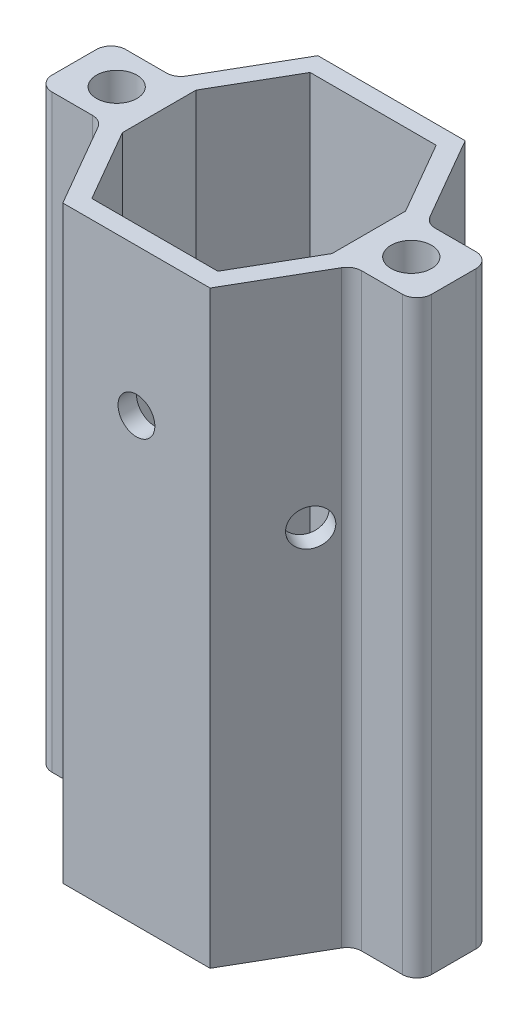
SolidWorks part; units mm, degrees
ref_plane "Front Plane" through (0, 0, 0) normal (0, 0, 1) x (1, 0, 0)
ref_plane "Top Plane" through (0, 0, 0) normal (0, 1, 0) x (1, 0, 0)
ref_plane "Right Plane" through (0, 0, 0) normal (1, 0, 0) x (0, 0, -1)
sketch "Sketch2" plane through (0, 0, 0) normal (0, 1, 0) x (1, 0, 0)
  line L0 (-12.7, 21.997) -> (12.7, 21.997)
  line L17 (12.7, 21.997) -> (25.4, 0)
  line L18 (25.4, 0) -> (12.7, -21.997)
  line L23 (12.7, -21.997) -> (-12.7, -21.997)
  line L24 (-12.7, -21.997) -> (-25.4, 0)
  line L25 (-25.4, 0) -> (-12.7, 21.997)
  line L26 (-10.8669, 18.822) -> (10.8669, 18.822)
  line L27 (10.8669, 18.822) -> (21.7338, 0)
  line L28 (21.7338, 0) -> (10.8669, -18.822)
  line L29 (10.8669, -18.822) -> (-10.8669, -18.822)
  line L30 (-10.8669, -18.822) -> (-21.7338, 0)
  line L31 (-21.7338, 0) -> (-10.8669, 18.822)
  line L32 (-25.4, 0) -> (25.4, 0) construction
  line L34 (-18.0677, -6.35) -> (-32.7323, -6.35)
  line L35 (-18.0677, -6.35) -> (-18.0677, 6.35)
  line L36 (-18.0677, 6.35) -> (-32.7323, 6.35)
  line L37 (-32.7323, -6.35) -> (-32.7323, 6.35)
  line L38 (-18.0677, -6.35) -> (-32.7323, 6.35) construction
  line L39 (-18.0677, 6.35) -> (-32.7323, -6.35) construction
  line L40 (18.0677, -6.35) -> (32.7323, -6.35)
  line L41 (18.0677, -6.35) -> (18.0677, 6.35)
  line L42 (18.0677, 6.35) -> (32.7323, 6.35)
  line L43 (32.7323, -6.35) -> (32.7323, 6.35)
  line L44 (18.0677, -6.35) -> (32.7323, 6.35) construction
  line L45 (18.0677, 6.35) -> (32.7323, -6.35) construction
  circle A0 centre (25.4, 0) radius 3.4925
  circle A1 centre (-25.4, 0) radius 3.4925
  point P0 (0, 0)
  point P3 (0, 21.997)
  point P5 (0, 0)
  point P20 (0, 0)
  point P29 (0, 0)
  dimension "D1" = 25.4
  dimension "D2" = 120
  dimension "D4" = 6.985
  dimension "D3" = 3.175
  dimension "D5" = 50.8
  dimension "D6" = 12.7
extrude "Boss-Extrude1" add sketch "Sketch2" along normal blind 101.6 contours A1 L25 L36 L37 L34 L24 | A0 L18 L40 L43 L42 L17 | L27 L42 L17 L0 L25 L36 L31 L26 | L40 L28 L29 L30 L34 L24 L23 L18 | A1 L24 L34 L30 L31 L36 L25 | L30 L35 L31 | A0 L17 L42 L27 L28 L40 L18 | L41 L28 L27
fillet "Fillet1" radius 2.54 8 edges at (-21.7338, 50.8, -6.35) (-32.7323, 50.8, -6.35) (-32.7323, 50.8, 6.35) (-21.7338, 50.8, 6.35) (21.7338, 50.8, 6.35) (32.7323, 50.8, 6.35) (32.7323, 50.8, -6.35) (21.7338, 50.8, -6.35)
sketch "Sketch9" plane through (0, 0, -21.997) normal (0, 0, 1) x (1, 0, 0)
  line L0 (-6.35, 6.35) -> (-6.35, 24.13) construction
  line L2 (-12.7, 0) -> (-21.0006, 0) construction
  line L4 (0, -24.1967) -> (0, 24.1967) construction
  circle A0 centre (-6.35, 6.35) radius 1
  circle A1 centre (-6.35, 24.13) radius 1
  circle A2 centre (6.35, 6.35) radius 1
  circle A3 centre (6.35, 24.13) radius 1
  circle A4 centre (-6.35, 49.53) radius 1
  circle A5 centre (-6.35, 31.75) radius 1
  circle A6 centre (6.35, 49.53) radius 1
  circle A7 centre (6.35, 31.75) radius 1
  dimension "D1" = 2
  dimension "D2" = 17.78
  dimension "D3" = 6.35
  dimension "D4" = 6.35
  dimension "D5" = 2
extrude "Cut-Extrude7" cut sketch "Sketch9" along normal up to surface (3.175 mm away) up to face at (0, 50.8, -18.822)
sketch "Sketch11" plane through (0, 0, -21.997) normal (0, 0, -1) x (-1, 0, 0)
  line L0 (12.7, 101.6) -> (-12.7, 101.6) construction
  circle A0 centre (0, 76.2) radius 3.175
  point P4 (0, 88.9)
  point P5 (0, 101.6)
  dimension "D2" = 6.35
  dimension "D1" = 25.4
extrude "Cut-Extrude8" cut sketch "Sketch11" against normal through all
sketch "Sketch12" plane through (-19.05, 0, -10.9985) normal (-0.866, 0, -0.5) x (-0.5, 0, 0.866)
  line L0 (3.9012, 101.6) -> (-12.7, 101.6) construction
  line L1 (-12.7, 101.6) -> (-12.7, 0) construction
  circle A0 centre (0, 63.5) radius 3.175
  point P2 (0, 0)
  dimension "D2" = 6.35
  dimension "D1" = 38.1
  dimension "D3" = 12.7
extrude "Cut-Extrude9" cut sketch "Sketch12" against normal through all
sketch "Sketch13" plane through (19.05, 0, -10.9985) normal (0.866, 0, -0.5) x (-0.5, 0, -0.866)
  line L0 (12.7, 101.6) -> (-3.9012, 101.6) construction
  line L1 (12.7, 101.6) -> (12.7, 0) construction
  circle A0 centre (0, 50.8) radius 3.175
  dimension "D1" = 6.35
  dimension "D2" = 50.8
  dimension "D3" = 12.7
extrude "Cut-Extrude10" cut sketch "Sketch13" against normal through all
